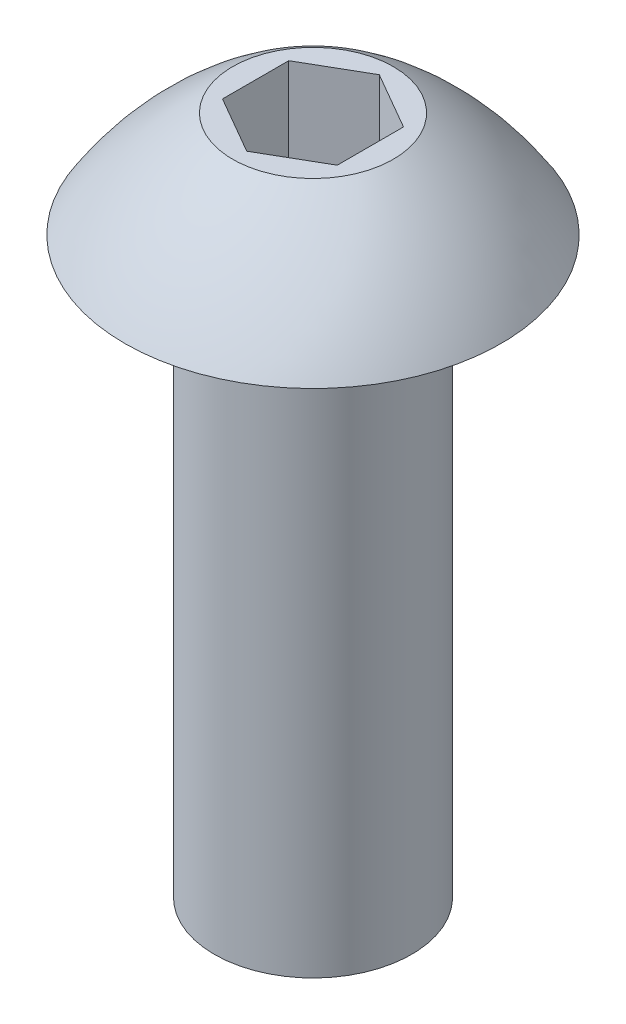
SolidWorks part; units mm, degrees
material "AISI Type 316L stainless steel"
ref_plane "Front Plane" through (0, 0, 0) normal (0, 0, 1) x (1, 0, 0)
ref_plane "Top Plane" through (0, 0, 0) normal (0, 1, 0) x (1, 0, 0)
ref_plane "Right Plane" through (0, 0, 0) normal (1, 0, 0) x (0, 0, -1)
sketch "Sketch1" plane through (0, 0, 0) normal (0, 0, 1) x (1, 0, 0)
  line L0 (-1.0922, 0) -> (-2.0828, 0)
  line L1 (-1.0922, 0) -> (-1.0922, -6.35)
  line L2 (0, -6.35) -> (0, 1.1684)
  line L3 (0, 1.1684) -> (-0.889, 1.1684)
  line L4 (-1.0922, -6.35) -> (0, -6.35)
  arc A0 (-2.0828, 0) -> (-0.889, 1.1684) centre (0.9356, -1.8899) cw
  dimension "D1" = 6.35
  dimension "D2" = 1.1684
  dimension "D3" = 2.0828
  dimension "D4" = 1.0922
  dimension "D5" = 0.889
revolve "Revolve1" add sketch "Sketch1" angle 360 about L2
sketch "Sketch2" plane through (0, 1.1684, 0) normal (0, 1, 0) x (1, 0, 0)
  line L0 (0, 0) -> (0, 0.7332) construction
  line L1 (-0.635, 0.3666) -> (-0.635, -0.3666)
  line L2 (-0.635, -0.3666) -> (0, -0.7332)
  line L3 (0, -0.7332) -> (0.635, -0.3666)
  line L4 (0.635, -0.3666) -> (0.635, 0.3666)
  line L5 (0.635, 0.3666) -> (0, 0.7332)
  line L6 (0, 0.7332) -> (-0.635, 0.3666)
  circle A0 centre (0, 0) radius 0.635 construction
  dimension "D1" = 1.27
extrude "Cut-Extrude1" cut sketch "Sketch2" against normal blind 1.27
